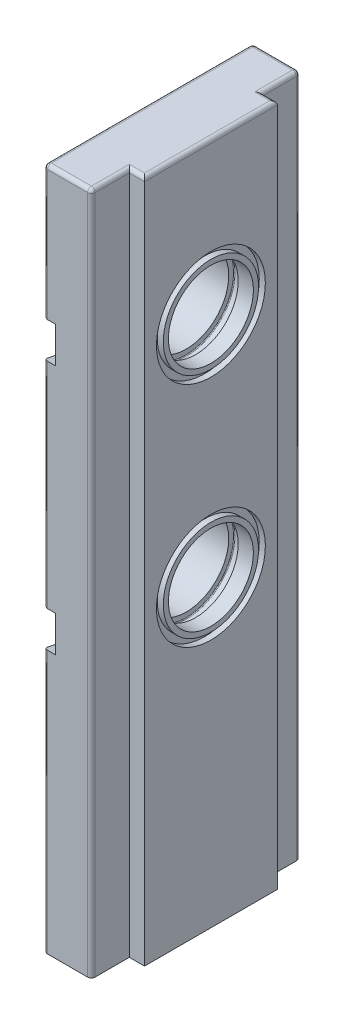
SolidWorks part; units mm, degrees
material "Perspex (TM) GS Acrylic Cast Sheet"
ref_plane "Front Plane" through (0, 0, 0) normal (0, 0, 1) x (1, 0, 0)
ref_plane "Top Plane" through (0, 0, 0) normal (0, 1, 0) x (1, 0, 0)
ref_plane "Right Plane" through (0, 0, 0) normal (1, 0, 0) x (0, 0, -1)
sketch "Sketch1" plane through (0, 0, 0) normal (0, 1, 0) x (1, 0, 0)
  line L0 (0, 0) -> (0, 55)
  line L1 (0, 55) -> (12.5, 55)
  line L2 (12.5, 55) -> (12.5, 45)
  line L3 (12.5, 45) -> (16.5, 45)
  line L4 (16.5, 45) -> (16.5, 10)
  line L5 (16.5, 10) -> (12.5, 10)
  line L6 (12.5, 10) -> (12.5, 0)
  line L7 (12.5, 0) -> (0, 0)
  line L8 (12.5, 45) -> (12.5, 10) construction
  dimension "D1" = 12.5
  dimension "D2" = 55
  dimension "D3" = 4
  dimension "D4" = 10
  dimension "D5" = 10
extrude "Boss-Extrude1" add sketch "Sketch1" along normal blind 180
sketch "Sketch3" plane through (16.5, 0, 0) normal (1, 0, 0) x (0, 0, -1)
  line L0 (10, 180) -> (45, 180) construction
  line L1 (27.5, 180) -> (27.5, 80.9914) construction
  circle A0 centre (27.5, 80) radius 11.2
  dimension "D1" = 100
  dimension "D3" = 22.4
extrude "Cut-Extrude1" cut sketch "Sketch3" against normal through all
ref_point "Point1"
ref_axis "Axis1" through (16.5, 80, -27.5) along (-1, 0, 0)
ref_plane "Plane1" through (0, 0, -27.5) normal (0, 0, 1) x (1, 0, 0)
sketch "Sketch11" plane through (0, 0, -27.5) normal (0, 0, 1) x (1, 0, 0)
  line L0 (12.5, 180) -> (12.5, 0) construction
  line L1 (10, 69.15) -> (12.5, 69.15)
  line L2 (10, 69.15) -> (10, 67.55)
  line L3 (10.2, 67.35) -> (12.3, 67.35)
  line L4 (12.5, 69.15) -> (12.5, 67.55)
  line L5 (16.5, 80) -> (-45.611, 80) construction
  line L6 (16.5, 180) -> (16.5, 0) construction
  line L7 (14.9, 67.45) -> (16.5, 67.45)
  line L8 (14.9, 67.45) -> (14.9, 65.65)
  line L9 (14.9, 65.65) -> (16.5, 65.65)
  line L10 (16.5, 67.45) -> (16.5, 65.65)
  arc A0 (12.3, 67.35) -> (12.5, 67.55) centre (12.3, 67.55) ccw
  arc A1 (10, 67.55) -> (10.2, 67.35) centre (10.2, 67.55) ccw
  point P16 (12.5, 67.35)
  point P19 (10, 67.35)
  dimension "D7" = 0.2
  dimension "D1" = 12.65
  dimension "D2" = 1.8
  dimension "D3" = 2.5
  dimension "D4" = 1.8
  dimension "D5" = 1.6
  dimension "D6" = 12.55
revolve "Cut-Revolve1" cut sketch "Sketch11" angle 360 about axis through (16.5, 80, -27.5) along (-1, 0, 0)
sketch "Sketch12" plane through (16.5, 0, 0) normal (1, 0, 0) x (0, 0, -1)
  line L0 (27.5, 80) -> (27.5, 180) construction
  line L1 (10, 180) -> (45, 180) construction
pattern_linear "LPattern1" count 2 spacing 60 along (0, 1, 0) of "Cut-Extrude1", "Cut-Revolve1"
hole_wizard "M6 Tapped Hole1" positions "Sketch14" profile "Sketch13" tap size "M6" standard "ISO"
sketch "Sketch14" plane through (0, 0, 0) normal (0, -1, 0) x (1, 0, 0)
  line L0 (12.5, 0) -> (12.5, -10) construction
  line L2 (6.5, -12.5) -> (6.5, -42.5) construction
  line L13 (6.5, -27.5) -> (0, -27.5) construction
  line L14 (0, -55) -> (0, 0) construction
  point P0 (6.5, -12.5)
  point P1 (6.5, -42.5)
  dimension "D1" = 6
  dimension "D2" = 30
sketch "Sketch13" plane through (6.5, 0, -12.5) normal (1, 0, 0) x (0, 0, -1)
  line L0 (0, 0) -> (0, 28.5022)
  line L1 (0, 28.5022) -> (2.5, 27)
  line L2 (2.5, 27) -> (2.5, 0)
  line L5 (2.5, 0) -> (0, 0)
  line L10 (0, 28.5022) -> (-2.5, 27) construction
  line L11 (0, -6.35) -> (0, 107.95) construction
  dimension "Tap Drill Dia." = 5
  dimension "Tap Drill Depth" = 27
  dimension "Drill Angle" = 118
cosmetic thread "Hole Thread1" parameters "D1"=22, "D2"=6
cosmetic thread "Hole Thread2" parameters "D1"=22, "D2"=6
sketch "Sketch15" plane through (0, 0, 0) normal (-1, 0, 0) x (0, 0, 1)
  line L0 (0, 180) -> (0, 0) construction
  line L1 (0, 144.75) -> (-9.5, 146.75)
  line L2 (0, 144.75) -> (0, 135.25)
  line L3 (0, 135.25) -> (-9.5, 133.25)
  line L4 (-9.5, 146.75) -> (-9.5, 133.25)
  line L5 (-27.5, 140) -> (-9.5, 140) construction
  line L6 (0, 78.8) -> (-9.5, 80.8)
  line L7 (-9.5, 80.8) -> (-9.5, 67.3)
  line L8 (-9.5, 67.3) -> (0, 69.3)
  line L9 (0, 69.3) -> (0, 78.8)
  line L10 (-55, 39.4) -> (-45.5, 41.4)
  line L11 (-55, 180) -> (-55, 0) construction
  line L12 (-45.5, 41.4) -> (-45.5, 27.9)
  line L13 (-45.5, 27.9) -> (-55, 29.9)
  line L14 (-55, 29.9) -> (-55, 39.4)
  line L15 (-30.8091, 69.3) -> (0, 69.3) construction
  line L16 (-30.8091, 69.3) -> (-45.5, 69.3) construction
  line L17 (-45.5, 69.3) -> (-45.5, 41.4) construction
  line L18 (-45.5, 27.9) -> (-45.5, 0) construction
  line L19 (-55, 0) -> (0, 0) construction
  line L21 (-9.5, 140) -> (0, 140) construction
  circle A0 centre (-27.5, 80) radius 11.2 construction
  dimension "D1" = 13.5
  dimension "D2" = 9.5
  dimension "D3" = 9.5
extrude "Cut-Extrude2" cut sketch "Sketch15" against normal blind 3
fillet "Fillet1" radius 1 15 edges at (0, 180, -27.5) (6.25, 180, -55) (12.5, 180, -50) (14.5, 180, -45) (16.5, 180, -27.5) (14.5, 180, -10) (12.5, 180, -5) (6.25, 180, 0) (0, 34.65, 0) (12.5, 90, -55) (0, 14.95, -55) (0, 109.7, -55) (0, 107.025, 0) (0, 162.375, 0) (12.5, 90, 0)
